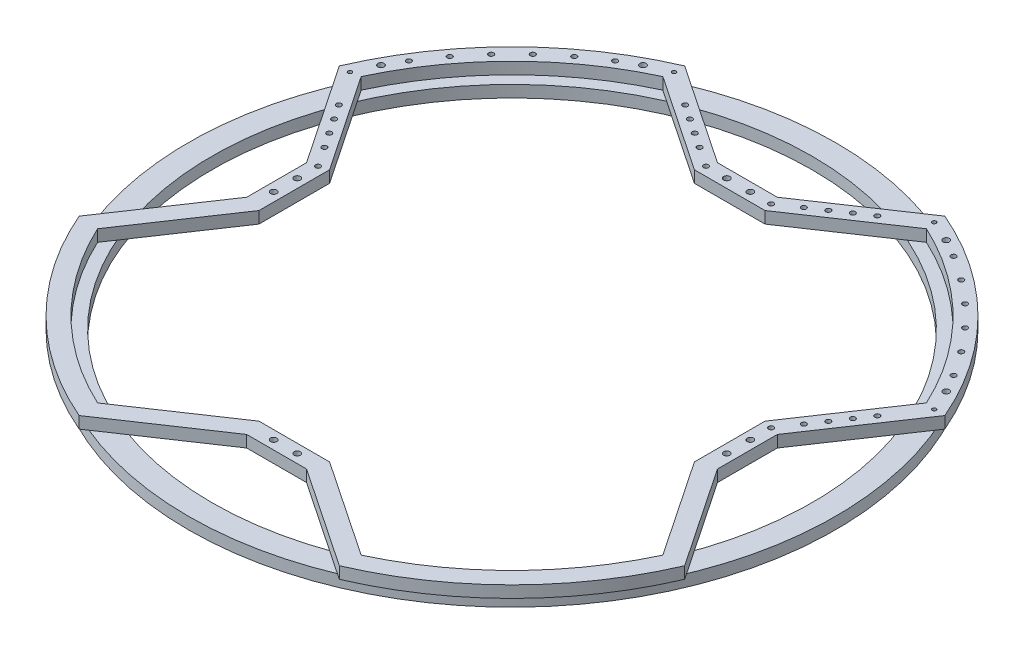
SolidWorks part; units mm, degrees
material "A-玻璃纤维"
ref_plane "前视基准面" through (0, 0, 0) normal (0, 0, 1) x (1, 0, 0)
ref_plane "上视基准面" through (0, 0, 0) normal (0, 1, 0) x (1, 0, 0)
ref_plane "右视基准面" through (0, 0, 0) normal (1, 0, 0) x (0, 0, -1)
sketch "草图1" plane through (0, 0, 0) normal (0, 1, 0) x (1, 0, 0)
  line L0 (0, 0) -> (275, 0) construction
  line L1 (0, 0) -> (0, 275) construction
  line L2 (0, 0) -> (194.4544, 194.4544) construction
  circle A0 centre (0, 0) radius 255
  circle A1 centre (0, 0) radius 275
  dimension "D1" = 510
  dimension "D2" = 20
  dimension "D3" = 45
extrude "凸台-拉伸1" add sketch "草图1" along normal blind 10
sketch "草图2" plane through (0, 10, 0) normal (0, 1, 0) x (1, 0, 0)
  line L0 (0, 0) -> (275, 0) construction
  line L1 (164.7559, 164.7559) -> (217.7889, 111.7229) construction
  line L2 (164.7559, 164.7559) -> (111.7229, 217.7889) construction
  line L3 (0, 0) -> (164.7559, 164.7559) construction
  line L4 (111.7229, 217.7889) -> (121.6224, 227.6884) construction
  line L5 (217.7889, 111.7229) -> (227.6884, 121.6224) construction
  line L6 (0, 0) -> (240.1716, 111.9938) construction
  line L7 (0, 0) -> (111.9938, 240.1716) construction
  line L8 (0, 0) -> (0, 275) construction
  line L9 (0, 185) -> (30, 185)
  line L10 (-110.5251, 257.2629) -> (-25.4233, 200)
  line L11 (111.9938, 240.1716) -> (30, 185)
  line L12 (0, 200) -> (-25.4233, 200)
  line L13 (240.1716, 111.9938) -> (185, 30)
  line L14 (185, 0) -> (185, 30)
  line L15 (-111.9938, 240.1716) -> (-30, 185)
  line L16 (0, 200) -> (25.4233, 200)
  line L17 (110.5251, 257.2629) -> (25.4233, 200)
  line L18 (257.2629, 110.5251) -> (200, 25.4233)
  line L19 (200, 0) -> (200, 25.4233)
  line L20 (0, 185) -> (-30, 185)
  line L21 (0, 185) -> (-30, 185) construction
  line L22 (0, 200) -> (-30, 200) construction
  line L23 (200, 0) -> (200, -1.5596) construction
  line L24 (185, 0) -> (185, -1.5596) construction
  line L25 (-200, -25.4233) -> (-200, 25.4233)
  line L26 (-257.2629, 110.5251) -> (-200, 25.4233)
  line L27 (-185, -30) -> (-185, 30)
  line L28 (-240.1716, 111.9938) -> (-185, 30)
  line L29 (185, 0) -> (185, -30)
  line L30 (200, 0) -> (200, -25.4233)
  line L31 (257.2629, -110.5251) -> (200, -25.4233)
  line L32 (240.1716, -111.9938) -> (185, -30)
  line L33 (164.7559, -164.7559) -> (111.7229, -217.7889) construction
  line L34 (110.5251, -257.2629) -> (25.4233, -200)
  line L35 (111.9938, -240.1716) -> (30, -185)
  line L36 (0, -185) -> (-30, -185)
  line L37 (0, -200) -> (-25.4233, -200)
  line L38 (0, -200) -> (25.4233, -200)
  line L39 (0, -185) -> (30, -185)
  line L40 (-111.9938, -240.1716) -> (-30, -185)
  line L41 (-110.5251, -257.2629) -> (-25.4233, -200)
  line L42 (-240.1716, -111.9938) -> (-185, -30)
  line L43 (-257.2629, -110.5251) -> (-200, -25.4233)
  circle A0 centre (0, 0) radius 275 construction
  arc A2 (111.9938, 240.1716) -> (240.1716, 111.9938) centre (0, 0) cw
  arc A3 (110.5251, 257.2629) -> (257.2629, 110.5251) centre (0, 0) cw
  arc A4 (-110.5251, 257.2629) -> (-257.2629, 110.5251) centre (0, 0) ccw
  arc A5 (-111.9938, 240.1716) -> (-240.1716, 111.9938) centre (0, 0) ccw
  arc A6 (110.5251, -257.2629) -> (257.2629, -110.5251) centre (0, 0) ccw
  arc A7 (111.9938, -240.1716) -> (240.1716, -111.9938) centre (0, 0) ccw
  arc A8 (-111.9938, -240.1716) -> (-240.1716, -111.9938) centre (0, 0) cw
  arc A9 (-110.5251, -257.2629) -> (-257.2629, -110.5251) centre (0, 0) cw
  point P60 (-185, 0)
  point P61 (-200, 0)
  dimension "D5" = 14
  dimension "D7" = 265
  dimension "D1" = 233
  dimension "D3" = 75
  dimension "D4" = 75
  dimension "D6" = 14
  dimension "D8" = 15
  dimension "D9" = 20
  dimension "D10" = 30
  dimension "D11" = 185
extrude "凸台-拉伸2" add sketch "草图2" along normal blind 10 separate body
sketch "草图8" plane through (0, 20, 0) normal (0, 1, 0) x (1, 0, 0)
  line L0 (0, 0) -> (-187.3833, 187.3833) construction
  line L1 (-243.7881, 137.7221) -> (-232.755, 126.689) construction
  line L2 (-137.7221, 243.7881) -> (-126.689, 232.755) construction
  line L3 (0, 0) -> (0, 200) construction
  line L4 (25.4233, 200) -> (-25.4233, 200) construction
  line L5 (-75, 233.3589) -> (-75, 215.2794) construction
  line L6 (75, 233.3589) -> (75, 215.2794) construction
  line L7 (-30, 185) -> (-111.9938, 240.1716) construction
  line L8 (-25.4233, 200) -> (-110.5251, 257.2629) construction
  line L9 (0, 0) -> (214.4019, 0) construction
  line L10 (200, -25.4233) -> (200, 25.4233) construction
  line L11 (-27.7116, 192.5) -> (-110.5251, 248.2231) construction
  line L12 (-10, 192.5) -> (-27.7116, 192.5) construction
  line L13 (-110.5251, 257.2629) -> (-110.5251, 248.2231) construction
  line L14 (-257.2629, 110.5251) -> (-248.2231, 110.5251) construction
  line L15 (-192.5, 27.7116) -> (-248.2231, 110.5251) construction
  line L16 (-233.3589, 75) -> (-215.2794, 75) construction
  line L17 (233.3589, 75) -> (215.2794, 75) construction
  line L18 (192.5, 27.7116) -> (248.2231, 110.5251) construction
  line L19 (257.2629, 110.5251) -> (248.2231, 110.5251) construction
  line L20 (243.7881, 137.7221) -> (232.755, 126.689) construction
  line L21 (137.7221, 243.7881) -> (126.689, 232.755) construction
  line L22 (0, 0) -> (187.3833, 187.3833) construction
  line L23 (110.5251, 257.2629) -> (110.5251, 248.2231) construction
  line L24 (27.7116, 192.5) -> (110.5251, 248.2231) construction
  line L25 (75, 233.3589) -> (75, 215.2794) construction
  line L26 (0, 185) -> (-20, 185) construction
  line L27 (30, 185) -> (-30, 185) construction
  line L28 (-20, 185) -> (-20, 200) construction
  line L29 (-25.4233, 200) -> (-20.6208, 196.7686) construction
  line L30 (-20.6208, 196.7686) -> (-28.9948, 184.3236) construction
  line L31 (-30, 185) -> (-28.9948, 184.3236) construction
  arc A0 (-111.9938, 240.1716) -> (-240.1716, 111.9938) centre (0, 0) ccw construction
  arc A1 (-110.5251, 257.2629) -> (-257.2629, 110.5251) centre (0, 0) ccw construction
  circle A2 centre (-10, 192.5) radius 2.65
  circle A3 centre (10, 192.5) radius 2.65
  circle A4 centre (-10, -192.5) radius 2.65
  circle A5 centre (10, -192.5) radius 2.65
  circle A6 centre (192.5, 10) radius 2.65
  circle A8 centre (192.5, -10) radius 2.65
  circle A9 centre (-192.5, 10) radius 2.65
  circle A10 centre (-192.5, -10) radius 2.65
  circle A11 centre (-110.5251, 248.2231) radius 1.65
  circle A12 centre (-27.7116, 192.5) radius 2.15
  circle A13 centre (-44.3049, 203.6652) radius 2.15
  circle A14 centre (-56.7499, 212.0391) radius 2.15
  circle A15 centre (-69.1949, 220.413) radius 2.15
  circle A16 centre (-81.6399, 228.787) radius 2.15
  arc A17 (-238.2716, 132.2055) -> (-128.8116, 240.1233) centre (0, 0) cw construction
  circle A18 centre (-143.8082, 231.4538) radius 2.15
  circle A19 centre (-164.4155, 217.2997) radius 2.15
  circle A20 centre (-183.6389, 201.3166) radius 2.15
  circle A21 centre (-201.3166, 183.6389) radius 2.15
  circle A22 centre (-217.2997, 164.4155) radius 2.15
  circle A23 centre (-231.4538, 143.8082) radius 2.15
  circle A24 centre (-128.8116, 240.1233) radius 2.65
  circle A25 centre (-240.1233, 128.8116) radius 2.65
  circle A26 centre (-228.787, 81.6399) radius 2.15
  circle A27 centre (-220.413, 69.1949) radius 2.15
  circle A28 centre (-212.0391, 56.7499) radius 2.15
  circle A29 centre (-203.6652, 44.3049) radius 2.15
  circle A30 centre (-192.5, 27.7116) radius 2.15
  circle A31 centre (-248.2231, 110.5251) radius 1.65
  circle A32 centre (192.5, 27.7116) radius 2.15
  circle A33 centre (248.2231, 110.5251) radius 1.65
  circle A34 centre (203.6652, 44.3049) radius 2.15
  circle A35 centre (212.0391, 56.7499) radius 2.15
  circle A36 centre (220.413, 69.1949) radius 2.15
  circle A37 centre (228.787, 81.6399) radius 2.15
  circle A38 centre (240.1233, 128.8116) radius 2.65
  circle A39 centre (231.4538, 143.8082) radius 2.15
  arc A40 (238.2716, 132.2055) -> (128.8116, 240.1233) centre (0, 0) ccw construction
  circle A41 centre (128.8116, 240.1233) radius 2.65
  circle A42 centre (201.3166, 183.6389) radius 2.15
  circle A43 centre (183.6389, 201.3166) radius 2.15
  circle A44 centre (164.4155, 217.2997) radius 2.15
  circle A45 centre (143.8082, 231.4538) radius 2.15
  circle A46 centre (81.6399, 228.787) radius 2.15
  circle A47 centre (69.1949, 220.413) radius 2.15
  circle A48 centre (56.7499, 212.0391) radius 2.15
  circle A49 centre (44.3049, 203.6652) radius 2.15
  circle A50 centre (110.5251, 248.2231) radius 1.65
  circle A51 centre (27.7116, 192.5) radius 2.15
  circle A52 centre (217.2997, 164.4155) radius 2.15
  circle A53 centre (0, 0) radius 165 construction
  dimension "D1" = 75
  dimension "D3" = 5.3
  dimension "D4" = 20
  dimension "D5" = 7.5
  dimension "D6" = 5.3
  dimension "D7" = 20
  dimension "D8" = 7.5
  dimension "D10" = 3.3
  dimension "D11" = 4.3
  dimension "D12" = 15
  dimension "D13" = 15
  dimension "D14" = 15
  dimension "D15" = 20
  dimension "D16" = 4.3
  dimension "D17" = 25
  dimension "D18" = 25
  dimension "D19" = 25
  dimension "D20" = 25
  dimension "D21" = 25
  dimension "D22" = 5.3
  dimension "D23" = 20
  dimension "D26" = 330
  dimension "D27" = 185
  dimension "D2" = 75
  dimension "D9" = 7.5
  dimension "D24" = 20
  dimension "D25" = 3.5
extrude "切除-拉伸1" cut sketch "草图8" against normal through all
